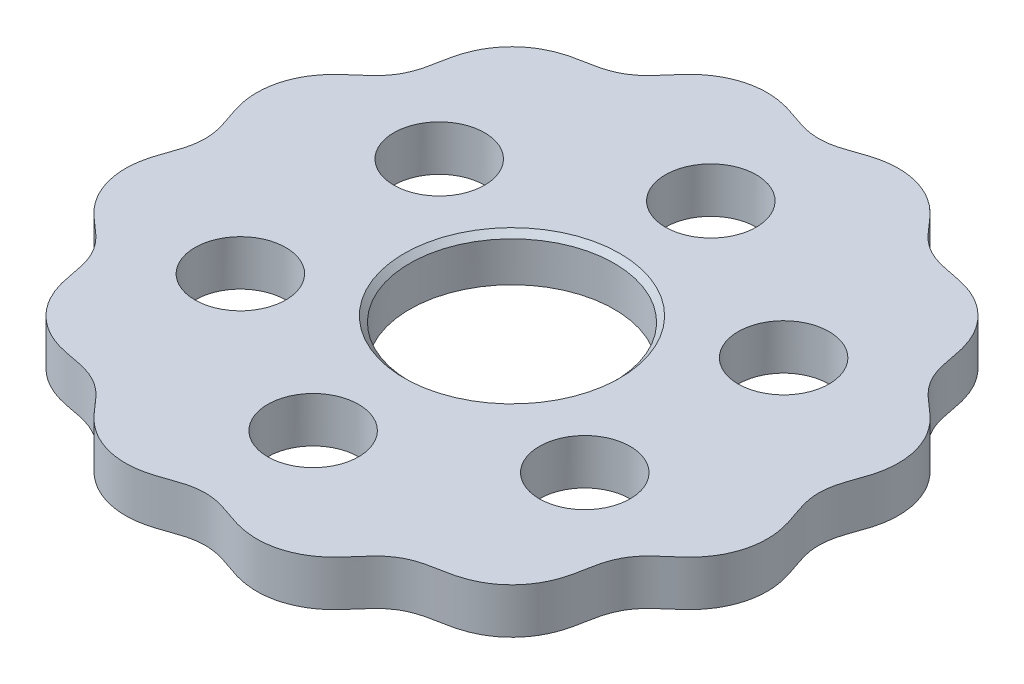
SolidWorks part; units mm, degrees
material "Polylactic Acid (PLA)"
ref_plane "Front Plane" through (0, 0, 0) normal (0, 0, 1) x (1, 0, 0)
ref_plane "Top Plane" through (0, 0, 0) normal (0, 1, 0) x (1, 0, 0)
ref_plane "Right Plane" through (0, 0, 0) normal (1, 0, 0) x (0, 0, -1)
sketch "Sketch1" plane through (0, 0, 0) normal (0, 1, 0) x (1, 0, 0)
  spline S0 degree 4 poles (22.6635, 15.5278) (22.694, 15.3764) (22.7597, 15.075) (22.9168, 14.4769) (23.2668, 13.6156) (23.8682, 12.704) (24.7627, 11.8447) (25.7313, 11.0803) (26.6185, 10.2145) (27.2551, 9.3344) (27.6787, 8.5074) (28.0266, 7.5556) (28.2156, 6.6706) (28.2671, 5.8227) (28.2081, 5.0347) (28.1283, 4.5049) (28.028, 4.036) (27.8872, 3.5336) (27.729, 3.0663) (27.5853, 2.6688) (27.4665, 2.3371) (27.3747, 2.0707) (27.2886, 1.8022) (27.2106, 1.5315) (27.1426, 1.2576) (27.0863, 0.982) (27.0484, 0.7371) (27.0246, 0.528) (27.0108, 0.3549) (27.0034, 0.2052) (26.9997, 0.0497) (26.9997, -0.038) (27.002, -0.1485) (27.0063, -0.2636) (27.0124, -0.3754) (27.0222, -0.4974) (27.0371, -0.6374) (27.0556, -0.7787) (27.0775, -0.9192) (27.1092, -1.0939) (27.1535, -1.3024) (27.2139, -1.5437) (27.293, -1.8166) (27.3802, -2.0871) (27.473, -2.3556) (27.593, -2.6899) (27.7377, -3.0908) (27.8962, -3.5622) (28.0634, -4.1672) (28.1925, -4.8421) (28.2747, -5.787) (28.1885, -6.9907) (27.811, -8.3475) (27.0846, -9.6473) (26.1861, -10.6718) (25.2382, -11.4719) (24.3726, -12.191) (23.6209, -13.0381) (23.063, -14.0252) (22.7232, -15.105) (22.5406, -16.2149) (22.3114, -17.4345) (21.8559, -18.719) (21.0787, -19.9817) (19.9443, -21.1081) (18.6762, -21.8764) (17.3888, -22.3233) (16.1685, -22.5473) (15.0588, -22.7333) (13.9816, -23.082) (12.9996, -23.6488) (12.1589, -24.4072) (11.4429, -25.2751) (10.6388, -26.22) (9.6083, -27.1117) (8.309, -27.8259) (6.7663, -28.2454) (5.2842, -28.2873) (3.944, -28.0398) (2.7732, -27.6285) (1.7207, -27.2316) (0.6156, -26.9859) (-0.5181, -26.9752) (-1.6276, -27.2025) (-2.6832, -27.5925) (-3.8501, -28.0135) (-5.1865, -28.2795) (-6.6753, -28.2589) (-8.2357, -27.8569) (-9.5567, -27.1493) (-10.6077, -26.2531) (-11.4243, -25.2991) (-12.1455, -24.4207) (-12.9931, -23.6523) (-13.9851, -23.0793) (-15.0742, -22.7291) (-16.1955, -22.5435) (-17.43, -22.3137) (-18.7318, -21.8518) (-20.0054, -21.0621) (-21.1341, -19.9121) (-21.8967, -18.6332) (-22.3348, -17.343) (-22.5539, -16.122) (-22.7438, -15.0128) (-23.1013, -13.9382) (-23.677, -12.9614) (-24.4421, -12.127) (-25.312, -11.4138) (-26.2537, -10.6057) (-27.1385, -9.5692) (-27.8436, -8.2648) (-28.2522, -6.7192) (-28.2837, -5.2368) (-28.0272, -3.8985) (-27.6111, -2.7296) (-27.2174, -1.6756) (-26.9805, -0.5684) (-26.9801, 0.5654) (-27.2164, 1.6727) (-27.61, 2.7268) (-28.0264, 3.8955) (-28.2835, 5.2338) (-28.2526, 6.7162) (-27.8447, 8.262) (-27.1402, 9.5666) (-26.2559, 10.6035) (-25.3144, 11.412) (-24.4444, 12.125) (-23.6789, 12.959) (-23.1026, 13.9354) (-22.7445, 15.0098) (-22.5543, 16.119) (-22.3356, 17.34) (-21.898, 18.6305) (-21.1359, 19.9097) (-20.0078, 21.0601) (-18.7346, 21.8505) (-17.433, 22.3129) (-16.1985, 22.5431) (-15.0772, 22.7284) (-13.9879, 23.0781) (-12.9955, 23.6505) (-12.1476, 24.4184) (-11.4261, 25.2967) (-10.6099, 26.251) (-9.5592, 27.1476) (-8.2386, 27.8558) (-6.6784, 28.2585) (-5.1895, 28.2798) (-3.853, 28.0143) (-2.686, 27.5936) (-1.6305, 27.2034) (-0.5212, 26.9755) (0.6126, 26.9855) (1.7178, 27.2307) (2.7704, 27.6274) (3.9411, 28.039) (5.2811, 28.2871) (6.7633, 28.2458) (8.3061, 27.8271) (9.6058, 27.1134) (10.6367, 26.2222) (11.441, 25.2775) (12.1568, 24.4095) (12.9971, 23.6506) (13.9788, 23.0832) (15.0559, 22.734) (16.1654, 22.5477) (17.3858, 22.324) (18.6734, 21.8778) (19.9419, 21.11) (21.0768, 19.9841) (21.8546, 18.7217) (22.3106, 17.4375) (22.5401, 16.2179) (22.7225, 15.1079) (23.0618, 14.028) (23.6191, 13.0406) (24.3704, 12.1931) (25.2358, 11.4738) (26.1839, 10.6739) (27.0829, 9.6498) (27.8098, 8.3504) (28.1879, 6.9938) (28.2746, 5.7903) (28.193, 4.8455) (28.0642, 4.1706) (27.8972, 3.5657) (27.7163, 3.0268) (27.521, 2.4935) (27.3561, 2.024) (27.2322, 1.6167) (27.1458, 1.2711) (27.0884, 0.9947) (27.0442, 0.7102) (27.0198, 0.4861) (27.0079, 0.3062) (27.0022, 0.1528) (26.9997, 0.042) (26.9996, -0.0456) (27.0032, -0.201) (27.0105, -0.3509) (27.0242, -0.5239) (27.0479, -0.733) (27.0856, -0.978) (27.1417, -1.2536) (27.2095, -1.5276) (27.2874, -1.7983) (27.3734, -2.0668) (27.4652, -2.3333) (27.5839, -2.665) (27.7277, -3.0625) (27.8859, -3.5297) (28.0537, -4.1271) (28.1849, -4.7916) (28.2731, -5.7196) (28.2068, -6.8215) (27.9166, -8.0047) (27.3482, -9.2051) (26.6211, -10.2114) (25.7344, -11.0777) (24.7659, -11.8422) (23.8708, -12.7009) (23.2688, -13.612) (22.9181, -14.473) (22.7607, -15.0711) (22.6948, -15.3725) (22.6643, -15.5239) knots 0 0 0 0 0 0.002811 0.005621 0.011242 0.016863 0.022484 0.028105 0.033725 0.039346 0.042156 0.044966 0.052152 0.055745 0.057541 0.059337 0.061903 0.064469 0.067035 0.068318 0.069601 0.070884 0.072167 0.07345 0.074733 0.076016 0.077299 0.07794 0.078582 0.079223 0.079864 0.080511 0.080835 0.081158 0.081805 0.082451 0.083098 0.083745 0.084391 0.085038 0.086332 0.087625 0.088918 0.090212 0.091505 0.092799 0.095386 0.097972 0.100559 0.10422 0.107881 0.115202 0.122411 0.12962 0.134741 0.139863 0.144984 0.150105 0.155226 0.160347 0.165468 0.170589 0.177799 0.185008 0.192217 0.199426 0.204547 0.209668 0.214789 0.21991 0.225032 0.230153 0.235274 0.240395 0.247604 0.254813 0.262022 0.269231 0.274352 0.279474 0.284595 0.289716 0.294837 0.299958 0.305079 0.310201 0.31741 0.324619 0.33194 0.339262 0.344435 0.349609 0.354783 0.359956 0.36513 0.370304 0.375477 0.380651 0.387973 0.395294 0.402503 0.409712 0.414833 0.419955 0.425076 0.430197 0.435318 0.440439 0.44556 0.450681 0.45789 0.465099 0.472309 0.479518 0.484639 0.48976 0.494881 0.500002 0.505123 0.510245 0.515366 0.520487 0.527696 0.534905 0.542114 0.549323 0.554444 0.559565 0.564686 0.569808 0.574929 0.58005 0.585171 0.590293 0.597502 0.604711 0.612032 0.619353 0.624527 0.629701 0.634875 0.640048 0.645222 0.650396 0.655569 0.660743 0.668064 0.675386 0.682595 0.689804 0.694925 0.700046 0.705168 0.710289 0.71541 0.720531 0.725652 0.730773 0.737982 0.745191 0.752401 0.75961 0.764731 0.769852 0.774973 0.780094 0.785215 0.790337 0.795458 0.800579 0.807788 0.814997 0.822206 0.829415 0.834536 0.839657 0.844778 0.849899 0.855021 0.860142 0.865263 0.870384 0.877594 0.884803 0.892123 0.895783 0.899443 0.90203 0.904616 0.907203 0.909789 0.912376 0.913669 0.914962 0.916256 0.917549 0.918842 0.919165 0.919489 0.920135 0.920777 0.921418 0.92206 0.922701 0.923984 0.925267 0.92655 0.927833 0.929116 0.930399 0.931682 0.932965 0.935531 0.938097 0.940662 0.944255 0.947848 0.955033 0.960654 0.966274 0.971895 0.977516 0.983137 0.988758 0.994379 0.997189 1 1 1 1 1 construction
  spline S1 degree 4 poles (27, 0) (27, -0.0298) (27.0005, -0.0746) (27.002, -0.1485) (27.0063, -0.2636) (27.0124, -0.3754) (27.0222, -0.4974) (27.0371, -0.6374) (27.0556, -0.7787) (27.0775, -0.9192) (27.1092, -1.0939) (27.1535, -1.3024) (27.2139, -1.5437) (27.293, -1.8166) (27.3802, -2.0871) (27.473, -2.3556) (27.593, -2.6899) (27.7377, -3.0908) (27.8962, -3.5622) (28.0634, -4.1672) (28.1925, -4.8421) (28.2747, -5.787) (28.1885, -6.9907) (27.811, -8.3475) (27.0846, -9.6473) (26.1861, -10.6718) (25.2382, -11.4719) (24.3726, -12.191) (23.6209, -13.0381) (23.063, -14.0252) (22.7232, -15.105) (22.5406, -16.2149) (22.3114, -17.4345) (21.8559, -18.719) (21.0787, -19.9817) (19.9443, -21.1081) (18.6762, -21.8764) (17.3888, -22.3233) (16.1685, -22.5473) (15.0588, -22.7333) (13.9816, -23.082) (12.9996, -23.6488) (12.1589, -24.4072) (11.4429, -25.2751) (10.6388, -26.22) (9.6083, -27.1117) (8.309, -27.8259) (6.7663, -28.2454) (5.2842, -28.2873) (3.944, -28.0398) (2.7732, -27.6285) (1.7207, -27.2316) (0.6156, -26.9859) (-0.5181, -26.9752) (-1.6276, -27.2025) (-2.6832, -27.5925) (-3.8501, -28.0135) (-5.1865, -28.2795) (-6.6753, -28.2589) (-8.2357, -27.8569) (-9.5567, -27.1493) (-10.6077, -26.2531) (-11.4243, -25.2991) (-12.1455, -24.4207) (-12.9931, -23.6523) (-13.9851, -23.0793) (-15.0742, -22.7291) (-16.1955, -22.5435) (-17.43, -22.3137) (-18.7318, -21.8518) (-20.0054, -21.0621) (-21.1341, -19.9121) (-21.8967, -18.6332) (-22.3348, -17.343) (-22.5539, -16.122) (-22.7438, -15.0128) (-23.1013, -13.9382) (-23.677, -12.9614) (-24.4421, -12.127) (-25.312, -11.4138) (-26.2537, -10.6057) (-27.1385, -9.5692) (-27.8436, -8.2648) (-28.2522, -6.7192) (-28.2837, -5.2368) (-28.0272, -3.8985) (-27.6111, -2.7296) (-27.2174, -1.6756) (-26.9805, -0.5684) (-26.9801, 0.5654) (-27.2164, 1.6727) (-27.61, 2.7268) (-28.0264, 3.8955) (-28.2835, 5.2338) (-28.2526, 6.7162) (-27.8447, 8.262) (-27.1402, 9.5666) (-26.2559, 10.6035) (-25.3144, 11.412) (-24.4444, 12.125) (-23.6789, 12.959) (-23.1026, 13.9354) (-22.7445, 15.0098) (-22.5543, 16.119) (-22.3356, 17.34) (-21.898, 18.6305) (-21.1359, 19.9097) (-20.0078, 21.0601) (-18.7346, 21.8505) (-17.433, 22.3129) (-16.1985, 22.5431) (-15.0772, 22.7284) (-13.9879, 23.0781) (-12.9955, 23.6505) (-12.1476, 24.4184) (-11.4261, 25.2967) (-10.6099, 26.251) (-9.5592, 27.1476) (-8.2386, 27.8558) (-6.6784, 28.2585) (-5.1895, 28.2798) (-3.853, 28.0143) (-2.686, 27.5936) (-1.6305, 27.2034) (-0.5212, 26.9755) (0.6126, 26.9855) (1.7178, 27.2307) (2.7704, 27.6274) (3.9411, 28.039) (5.2811, 28.2871) (6.7633, 28.2458) (8.3061, 27.8271) (9.6058, 27.1134) (10.6367, 26.2222) (11.441, 25.2775) (12.1568, 24.4095) (12.9971, 23.6506) (13.9788, 23.0832) (15.0559, 22.734) (16.1654, 22.5477) (17.3858, 22.324) (18.6734, 21.8778) (19.9419, 21.11) (21.0768, 19.9841) (21.8546, 18.7217) (22.3106, 17.4375) (22.5401, 16.2179) (22.7225, 15.1079) (23.0618, 14.028) (23.6191, 13.0406) (24.3704, 12.1931) (25.2358, 11.4738) (26.1839, 10.6739) (27.0829, 9.6498) (27.8098, 8.3504) (28.1879, 6.9938) (28.2746, 5.7903) (28.193, 4.8455) (28.0642, 4.1706) (27.8972, 3.5657) (27.7163, 3.0268) (27.521, 2.4935) (27.3561, 2.024) (27.2322, 1.6167) (27.1458, 1.2711) (27.0884, 0.9947) (27.0442, 0.7102) (27.0198, 0.4861) (27.0079, 0.3062) (27.0022, 0.1528) (27.0005, 0.0787) (27, 0.0339) (27, 0.0041) knots 0.079864 0.079864 0.079864 0.079864 0.079864 0.080511 0.080835 0.081158 0.081805 0.082451 0.083098 0.083745 0.084391 0.085038 0.086332 0.087625 0.088918 0.090212 0.091505 0.092799 0.095386 0.097972 0.100559 0.10422 0.107881 0.115202 0.122411 0.12962 0.134741 0.139863 0.144984 0.150105 0.155226 0.160347 0.165468 0.170589 0.177799 0.185008 0.192217 0.199426 0.204547 0.209668 0.214789 0.21991 0.225032 0.230153 0.235274 0.240395 0.247604 0.254813 0.262022 0.269231 0.274352 0.279474 0.284595 0.289716 0.294837 0.299958 0.305079 0.310201 0.31741 0.324619 0.33194 0.339262 0.344435 0.349609 0.354783 0.359956 0.36513 0.370304 0.375477 0.380651 0.387973 0.395294 0.402503 0.409712 0.414833 0.419955 0.425076 0.430197 0.435318 0.440439 0.44556 0.450681 0.45789 0.465099 0.472309 0.479518 0.484639 0.48976 0.494881 0.500002 0.505123 0.510245 0.515366 0.520487 0.527696 0.534905 0.542114 0.549323 0.554444 0.559565 0.564686 0.569808 0.574929 0.58005 0.585171 0.590293 0.597502 0.604711 0.612032 0.619353 0.624527 0.629701 0.634875 0.640048 0.645222 0.650396 0.655569 0.660743 0.668064 0.675386 0.682595 0.689804 0.694925 0.700046 0.705168 0.710289 0.71541 0.720531 0.725652 0.730773 0.737982 0.745191 0.752401 0.75961 0.764731 0.769852 0.774973 0.780094 0.785215 0.790337 0.795458 0.800579 0.807788 0.814997 0.822206 0.829415 0.834536 0.839657 0.844778 0.849899 0.855021 0.860142 0.865263 0.870384 0.877594 0.884803 0.892123 0.895783 0.899443 0.90203 0.904616 0.907203 0.909789 0.912376 0.913669 0.914962 0.916256 0.917549 0.918842 0.919165 0.919489 0.920135 0.920135 0.920135 0.920135 0.920135
  spline S2 degree 1 poles (27, 0.0041) (27, 0) knots 0 0 1 1
extrude "Boss-Extrude1" add sketch "Sketch1" along normal blind 4
sketch "Sketch2" plane through (0, 4, 0) normal (0, 1, 0) x (1, 0, 0)
  circle A0 centre (0, 0) radius 9
  dimension "D1" = 18
extrude "Cut-Extrude1" cut sketch "Sketch2" against normal blind 4
sketch "Sketch3" plane through (0, 4, 0) normal (0, 1, 0) x (1, 0, 0)
  circle A0 centre (0, 0) radius 17.5 construction
  circle A1 centre (0, 17.5) radius 4
  circle A2 centre (15.1554, 8.75) radius 4
  circle A3 centre (15.1554, -8.75) radius 4
  circle A4 centre (0, -17.5) radius 4
  circle A5 centre (-15.1554, -8.75) radius 4
  circle A6 centre (-15.1554, 8.75) radius 4
  point P17 (0, 0)
  dimension "D1" = 35
  dimension "D2" = 8
  dimension "D3" = 6
extrude "Cut-Extrude2" cut sketch "Sketch3" against normal blind 10
chamfer "Chamfer1" distance 0.5 angle 45 1 edges at (0, 4, 9)
